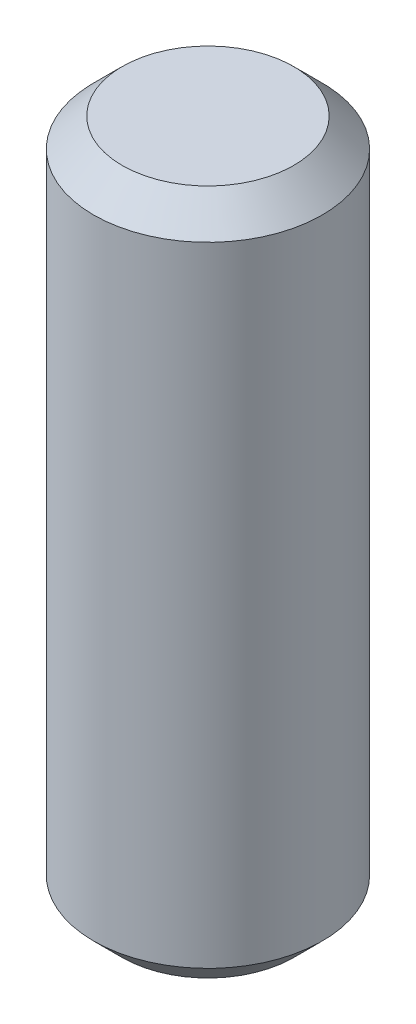
SolidWorks part; units mm, degrees
ref_plane "Front Plane" through (0, 0, 0) normal (0, 0, 1) x (1, 0, 0)
ref_plane "Top Plane" through (0, 0, 0) normal (0, 1, 0) x (1, 0, 0)
ref_plane "Right Plane" through (0, 0, 0) normal (1, 0, 0) x (0, 0, -1)
sketch "Sketch2" plane through (0, 0, 0) normal (0, 1, 0) x (1, 0, 0)
  circle A0 centre (0, 0) radius 1
  dimension "D1" = 2
extrude "Boss-Extrude1" add sketch "Sketch2" along normal blind 6
chamfer "Chamfer1" distance 0.25 angle 45 2 edges at (0, 0, 1) (0, 6, 1)
